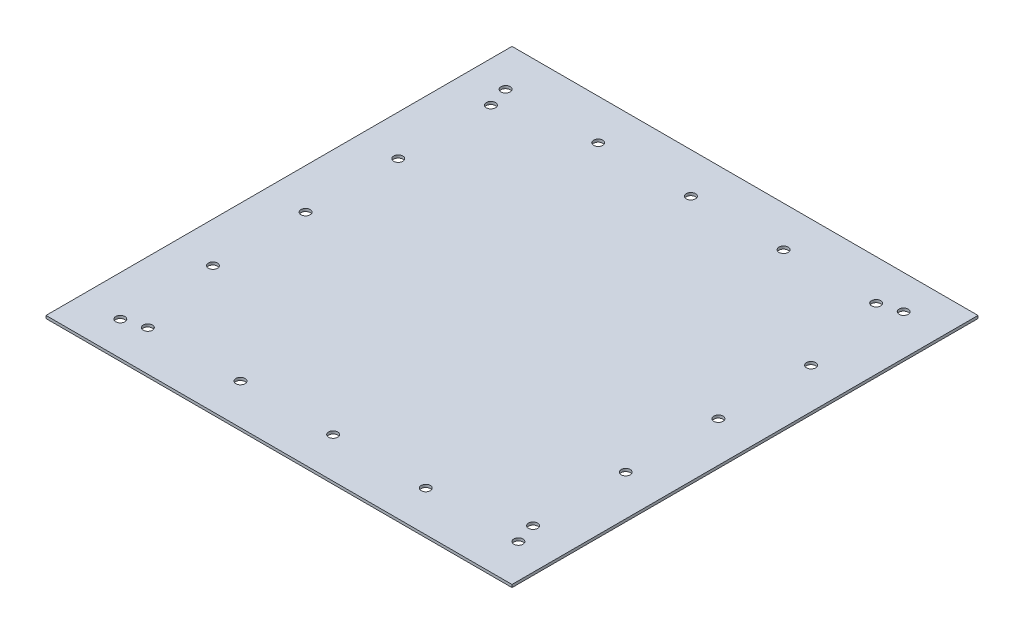
SolidWorks part; units mm, degrees
ref_plane "Front Plane" through (0, 0, 0) normal (0, 0, 1) x (1, 0, 0)
ref_plane "Top Plane" through (0, 0, 0) normal (0, 1, 0) x (1, 0, 0)
ref_plane "Right Plane" through (0, 0, 0) normal (1, 0, 0) x (0, 0, -1)
sketch "Sketch1" plane through (0, 0, 0) normal (0, 1, 0) x (1, 0, 0)
  line L1 (-254, -254) -> (254, -254)
  line L2 (-254, -254) -> (-254, 254)
  line L3 (-254, 254) -> (254, 254)
  line L4 (254, -254) -> (254, 254)
  line L5 (-254, -254) -> (254, 254) construction
  line L6 (-254, 254) -> (254, -254) construction
  point P0 (0, 0)
  dimension "D1" = 508
  dimension "D2" = 508
extrude "Boss-Extrude1" add sketch "Sketch1" along normal blind 3
sketch "Sketch3" plane through (0, 0, 0) normal (0, -1, 0) x (1, 0, 0)
  line L1 (225, -225) -> (-225, -225) construction
  line L2 (225, -225) -> (225, 225) construction
  line L3 (225, 225) -> (-225, 225) construction
  line L4 (-225, -225) -> (-225, 225) construction
  line L5 (225, -225) -> (-225, 225) construction
  line L6 (225, 225) -> (-225, -225) construction
  line L7 (-254, 254) -> (254, -254) construction
  line L8 (210, 210) -> (-210, 210) construction
  line L9 (-210, -210) -> (-210, 210) construction
  line L10 (210, -210) -> (-210, -210) construction
  line L11 (210, -210) -> (210, 210) construction
  circle A0 centre (217, 210) radius 5
  circle A1 centre (116, 210) radius 5
  circle A2 centre (15, 210) radius 5
  circle A3 centre (-86, 210) radius 5
  circle A4 centre (-187, 210) radius 5
  circle A5 centre (-210, 217) radius 5
  circle A6 centre (-210, 116) radius 5
  circle A7 centre (-210, 15) radius 5
  circle A8 centre (-210, -86) radius 5
  circle A9 centre (-210, -187) radius 5
  circle A10 centre (-217, -210) radius 5
  circle A11 centre (-116, -210) radius 5
  circle A12 centre (-15, -210) radius 5
  circle A13 centre (86, -210) radius 5
  circle A14 centre (187, -210) radius 5
  circle A15 centre (210, -217) radius 5
  circle A16 centre (210, -116) radius 5
  circle A17 centre (210, -15) radius 5
  circle A18 centre (210, 86) radius 5
  circle A19 centre (210, 187) radius 5
  point P0 (0, 0)
  dimension "D1" = 450
  dimension "D5" = 5
  dimension "D2" = 8
  dimension "D4" = 8
  dimension "D6" = 8
  dimension "D8" = 8
  dimension "D3" = 5
  dimension "D7" = 5
  dimension "D9" = 5
extrude "Cut-Extrude1" cut sketch "Sketch3" against normal blind 3
